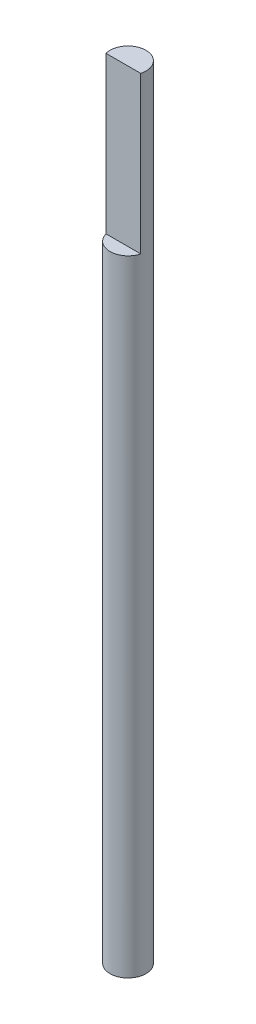
SolidWorks part; units mm, degrees
ref_plane "Front Plane" through (0, 0, 0) normal (0, 0, 1) x (1, 0, 0)
ref_plane "Top Plane" through (0, 0, 0) normal (0, 1, 0) x (1, 0, 0)
ref_plane "Right Plane" through (0, 0, 0) normal (1, 0, 0) x (0, 0, -1)
sketch "Sketch1" plane through (0, 0, 0) normal (0, 1, 0) x (1, 0, 0)
  circle A0 centre (0, 0) radius 2.921
  dimension "D1" = 5.842
extrude "Boss-Extrude1" add sketch "Sketch1" along normal blind 127 contours A0
sketch "Sketch2" plane through (0, 127, 0) normal (0, 1, 0) x (1, 0, 0)
  line L1 (-2.822, -0.7541) -> (2.8626, -0.7541)
  line L2 (-2.822, -0.7541) -> (-2.822, -3.1264)
  line L3 (-2.822, -3.1264) -> (2.8626, -3.1264)
  line L4 (2.8626, -0.7541) -> (2.8626, -3.1264)
  circle A0 centre (0, 0) radius 2.921 construction
extrude "Cut-Extrude1" cut sketch "Sketch2" against normal blind 25.4
